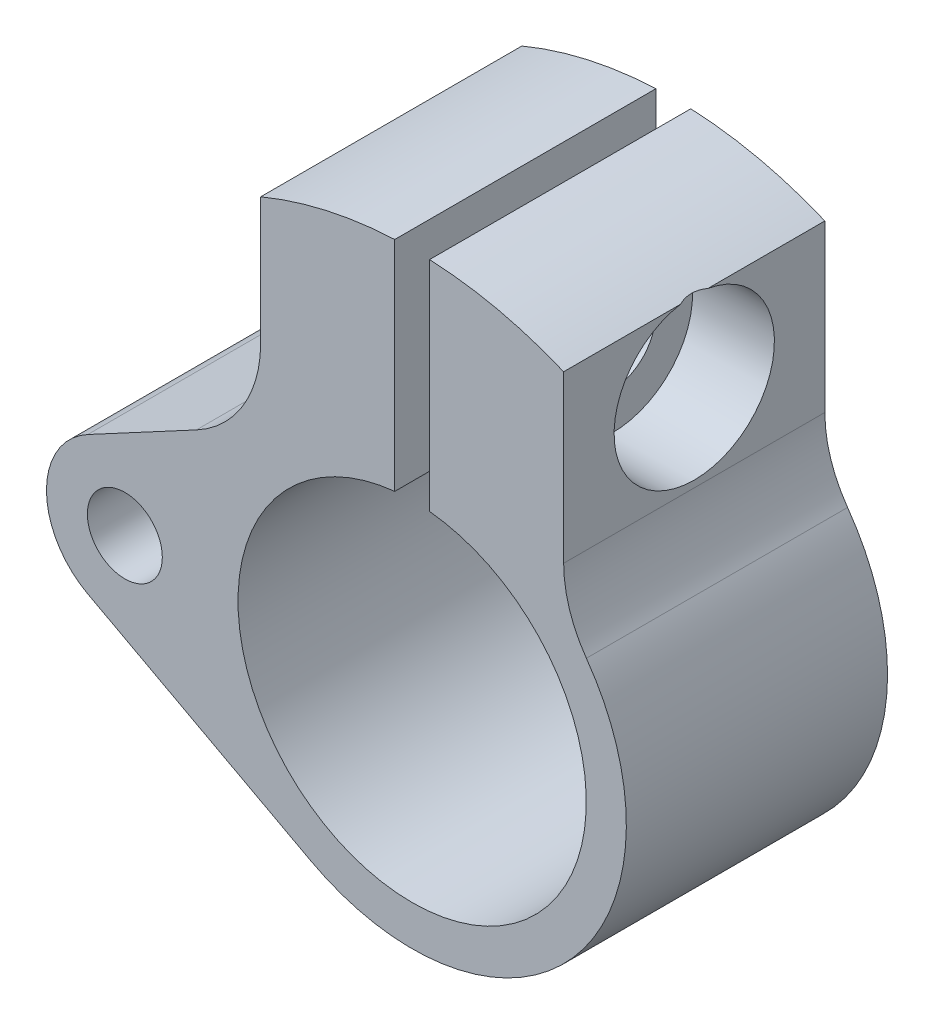
SolidWorks part; units mm, degrees
material "6061-T6 (SS)"
ref_plane "Front" through (0, 0, 0) normal (0, 0, 1) x (1, 0, 0)
ref_plane "Top" through (0, 0, 0) normal (0, 1, 0) x (1, 0, 0)
ref_plane "Right" through (0, 0, 0) normal (1, 0, 0) x (0, 0, -1)
sketch "Sketch1" plane through (0, 0, 0) normal (0, 0, 1) x (1, 0, 0)
  line L0 (11.2242, 18.1032) -> (11.2242, 11.2452) construction
  line L1 (0, 0) -> (0, 26.8991) construction
  line L2 (-8.7, 20.7499) -> (-8.7, 9.291)
  line L3 (-4.7014, 28.2036) -> (1.6486, 28.2036) construction
  line L4 (-8.7, 20.7499) -> (-8.7, 29.3993) construction
  line L5 (8.7, 20.7499) -> (8.7, 8.6948)
  line L6 (0, 0) -> (-5.5167, 0) construction
  line L7 (-18.6273, 3.9654) -> (-8.7, 9.291)
  line L8 (-18.6273, -3.9654) -> (-5.8145, -10.8389)
  circle A0 centre (0, 0) radius 10
  arc A1 (-5.8145, -10.8389) -> (8.7, 8.6948) centre (0, 0) ccw
  arc A2 (8.7, 20.7499) -> (-8.7, 20.7499) centre (0, 0) ccw
  arc A3 (-18.6273, 3.9654) -> (-18.6273, -3.9654) centre (-16.5, 0) ccw
  circle A4 centre (0, 0) radius 12 construction
  circle A5 centre (0, 0) radius 12.3 construction
  dimension "D1" = 20
  dimension "D2" = 24.6
  dimension "D4" = 45
  dimension "D7" = 9
  dimension "D8" = 24
  dimension "D3" = 6.858
  dimension "D5" = 6.35
  dimension "D6" = 17.4
extrude "Boss-Extrude1" add sketch "Sketch1" along normal mid plane 15
fillet "Fillet1" radius 7 2 edges at (-8.7, 9.291, 0) (8.7, 8.6948, 0)
sketch "Sketch2" plane through (0, 0, 7.5) normal (0, 0, 1) x (1, 0, 0)
  line L0 (0, 0) -> (0, 30.19) construction
  line L1 (-1, 22.4778) -> (-1, 9.9499)
  line L2 (1, 22.4778) -> (1, 9.9499)
  arc A0 (8.7, 20.7499) -> (-8.7, 20.7499) centre (0, 0) ccw construction
  arc A1 (1, 22.4778) -> (-1, 22.4778) centre (0, 0) ccw
  circle A2 centre (0, 0) radius 10 construction
  arc A3 (1, 9.9499) -> (-1, 9.9499) centre (0, 0) ccw
  dimension "D1" = 2
extrude "Cut-Extrude1" cut sketch "Sketch2" against normal through all
sketch "Sketch3" plane through (1, 0, 0) normal (1, 0, 0) x (0, 0, -1)
  line L0 (-7.5, 22.4778) -> (7.5, 9.9499) construction
  circle A0 centre (0, 16.2138) radius 4.6037
  point P6 (0, 16.2138)
  dimension "D1" = 9.2075
extrude "Cut-Extrude2" cut sketch "Sketch3" along normal blind 15 from offset 3
hole_wizard "#8 Clearance Hole1" positions "Sketch5" profile "Sketch4" hole size "#8" standard "Ansi Inch" end condition up to next
sketch "Sketch5" plane through (4, 0, 0) normal (1, 0, 0) x (0, 0, -1)
  arc A1 (-0.7862, 20.7499) -> (0.7862, 20.7499) centre (0, 16.2138) ccw construction
  point P0 (0, 16.2138)
sketch "Sketch4" plane through (4, 16.2138, 0) normal (0, 1, 0) x (0, 0, -1)
  line L0 (0, 0) -> (0, 3)
  line L1 (0, 3) -> (2.4574, 3)
  line L2 (2.4574, 3) -> (2.4574, 0)
  line L5 (2.4574, 0) -> (0, 0)
  line L11 (0, -6.35) -> (0, 107.95) construction
  dimension "Thru Hole Dia." = 4.9149
  dimension "Thru Hole Depth" = 3
hole_wizard "#8-32 Tapped Hole1" positions "Sketch7" profile "Sketch6" tap size "#8-32" standard "Ansi Inch" end condition through all
sketch "Sketch7" plane through (-1, 1.0979, -6.2424) normal (-1, 0, 0) x (0, 0, 1)
  circle A0 centre (6.2424, 15.116) radius 2.4574 construction
  point P0 (6.2424, 15.116)
sketch "Sketch6" plane through (-1, 16.2138, 0) normal (0, 1, 0) x (0, 0, -1)
  line L0 (0, 0) -> (0, 20)
  line L1 (0, 20) -> (1.7272, 20)
  line L2 (1.7272, 20) -> (1.7272, 0)
  line L5 (1.7272, 0) -> (0, 0)
  line L11 (0, -6.35) -> (0, 107.95) construction
  dimension "Thru Tap Drill Dia." = 3.4544
  dimension "Thru Tap Drill Depth" = 20
cosmetic thread "Hole Thread3" parameters "D1"=7.7, "D2"=4.1656
hole_wizard "#8 Clearance Hole2" positions "Sketch11" profile "Sketch10" hole size "#8" standard "Ansi Inch" end condition up to next
sketch "Sketch11" plane through (0, 0, 7.5) normal (0, 0, 1) x (1, 0, 0)
  arc A0 (-18.6273, 3.9654) -> (-18.6273, -3.9654) centre (-16.5, 0) ccw construction
  point P0 (-16.5, 0)
sketch "Sketch10" plane through (-16.5, 0, 7.5) normal (1, 0, 0) x (0, -1, 0)
  line L0 (0, 0) -> (0, 15)
  line L1 (0, 15) -> (2.1526, 15)
  line L2 (2.1526, 15) -> (2.1526, 0)
  line L5 (2.1526, 0) -> (0, 0)
  line L11 (0, -6.35) -> (0, 107.95) construction
  dimension "Thru Hole Dia." = 4.3053
  dimension "Thru Hole Depth" = 15
